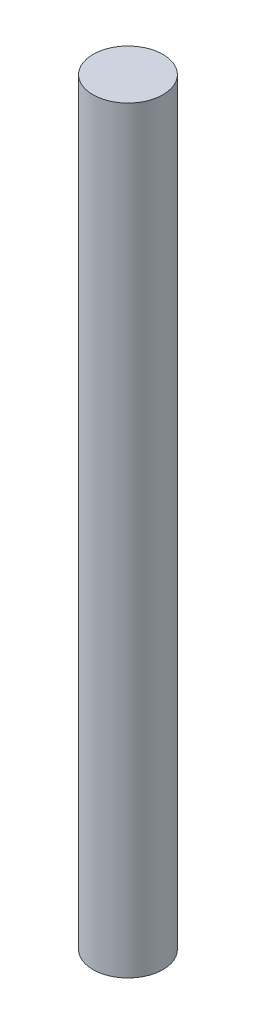
SolidWorks part; units mm, degrees
ref_plane "Front Plane" through (0, 0, 0) normal (0, 0, 1) x (1, 0, 0)
ref_plane "Top Plane" through (0, 0, 0) normal (0, 1, 0) x (1, 0, 0)
ref_plane "Right Plane" through (0, 0, 0) normal (1, 0, 0) x (0, 0, -1)
sketch "Sketch1" plane through (0, 0, 0) normal (0, 1, 0) x (1, 0, 0)
  circle A0 centre (0, 0) radius 3
  dimension "D1" = 6
extrude "Boss-Extrude1" add sketch "Sketch1" along normal blind 65
